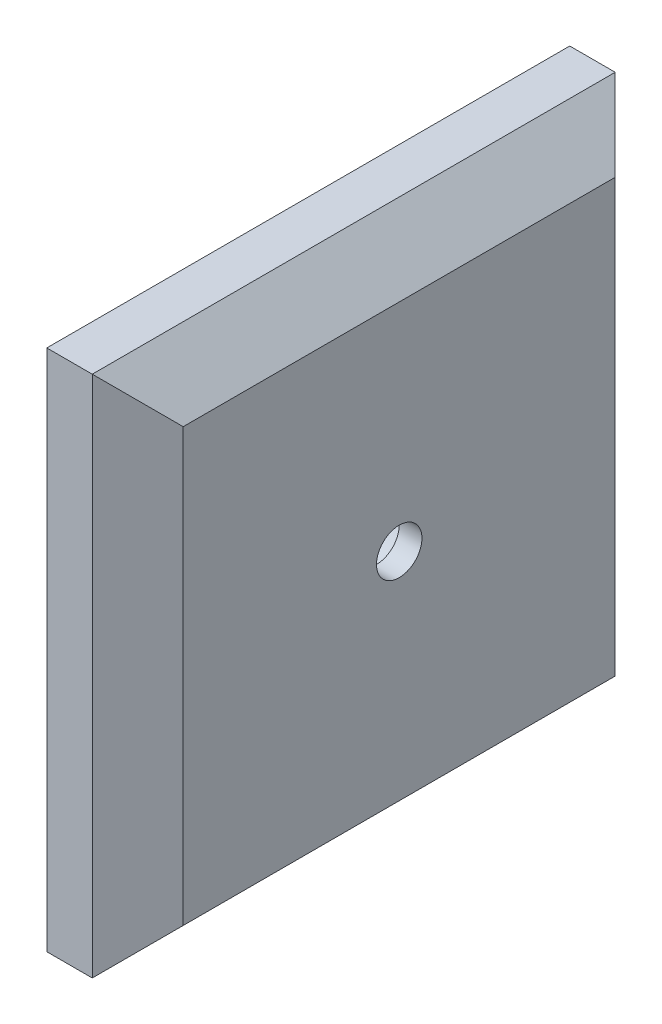
SolidWorks part; units mm, degrees
material "1023 Carbon Steel Sheet (SS)"
ref_plane "Front Plane" through (0, 0, 0) normal (0, 0, 1) x (1, 0, 0)
ref_plane "Top Plane" through (0, 0, 0) normal (0, 1, 0) x (1, 0, 0)
ref_plane "Right Plane" through (0, 0, 0) normal (1, 0, 0) x (0, 0, -1)
sketch "Sketch2" plane through (0, 0, 0) normal (1, 0, 0) x (0, 0, -1)
  line L1 (-36.5125, 36.5125) -> (36.5125, 36.5125)
  line L2 (-36.5125, 36.5125) -> (-36.5125, -36.5125)
  line L3 (-36.5125, -36.5125) -> (36.5125, -36.5125)
  line L4 (36.5125, 36.5125) -> (36.5125, -36.5125)
  line L5 (-36.5125, 36.5125) -> (36.5125, -36.5125) construction
  line L6 (-36.5125, -36.5125) -> (36.5125, 36.5125) construction
  point P0 (0, 0)
  dimension "D1" = 73.025
extrude "Boss-Extrude1" add sketch "Sketch2" along normal blind 12.7
chamfer "Chamfer1" distance 6.35 4 edges at (12.7, 0, -36.5125) (12.7, -36.5125, 0) (12.7, 0, 36.5125) (12.7, 36.5125, 0)
ref_plane "Plane3" through (6.35, 36.5125, -36.5125) normal (-1, 0, 0) x (0, 0, 1)
sketch "Sketch5" plane through (12.7, 0, 0) normal (1, 0, 0) x (0, 0, -1)
  circle A0 centre (0, 0) radius 3.175
  dimension "D1" = 6.35
extrude "Cut-Extrude1" cut sketch "Sketch5" against normal blind 3.175
sketch "Sketch6" plane through (0, 0, 0) normal (-1, 0, 0) x (0, 0, 1)
  circle A0 centre (0, 0) radius 6.35
  dimension "D1" = 12.7
extrude "Cut-Extrude2" cut sketch "Sketch6" against normal blind 9.525
